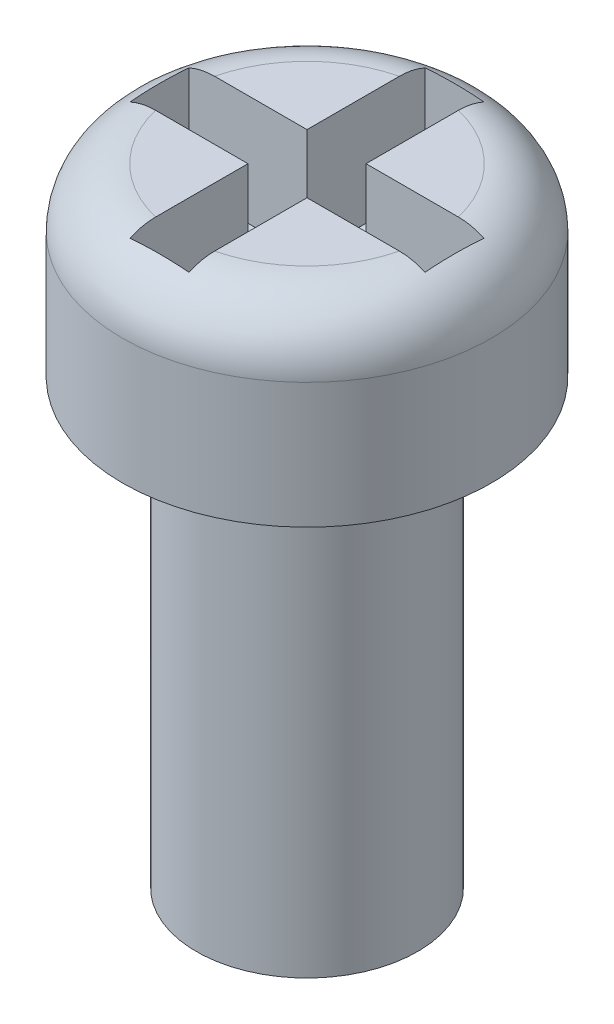
SolidWorks part; units mm, degrees
ref_plane "Alzado" through (0, 0, 0) normal (0, 0, 1) x (1, 0, 0)
ref_plane "Planta" through (0, 0, 0) normal (0, 1, 0) x (1, 0, 0)
ref_plane "Vista lateral" through (0, 0, 0) normal (1, 0, 0) x (0, 0, -1)
sketch "Croquis1" plane through (0, 0, 0) normal (0, 0, 1) x (1, 0, 0)
  line L0 (0, 0) -> (0, 8.5) construction
  line L1 (0, 0) -> (-1.5, 0)
  line L2 (-1.5, 0) -> (-1.5, 6)
  line L3 (-1.5, 6) -> (-2.5, 6)
  line L4 (-2.5, 6) -> (-2.5, 8.5)
  line L5 (-2.5, 8.5) -> (0, 8.5)
  line L6 (0, 0) -> (0, 8.5)
  dimension "D1" = 6
  dimension "D2" = 2.5
  dimension "D3" = 2.5
  dimension "D4" = 1.5
revolve "Revolución1" add sketch "Croquis1" angle 360 about L0
fillet "Redondeo1" radius 0.8 1 edges at (0, 8.5, -2.5)
sketch "Croquis2" plane through (0, 8.5, 0) normal (0, 1, 0) x (1, 0, 0)
  line L4 (0, -2) -> (0, 2) construction
  line L5 (-2, 0) -> (2, 0) construction
  line L6 (0.4, -2) -> (0.4, -0.4)
  line L7 (-2, -0.4) -> (-0.4, -0.4)
  line L8 (-0.4, -2) -> (-0.4, -0.4)
  line L9 (-2, 0.4) -> (-0.4, 0.4)
  line L10 (0.4, -2) -> (-0.4, -2)
  line L11 (0.4, 2) -> (-0.4, 2)
  line L12 (-2, -0.4) -> (-2, 0.4)
  line L13 (2, -0.4) -> (2, 0.4)
  line L14 (-0.4, 0.4) -> (-0.4, 2)
  line L15 (-0.4, -2) -> (-0.4, 2) construction
  line L16 (0.4, 0.4) -> (2, 0.4)
  line L17 (-2, 0.4) -> (2, 0.4) construction
  line L18 (0.4, 0.4) -> (0.4, 2)
  line L19 (0.4, -2) -> (0.4, 2) construction
  line L20 (0.4, -0.4) -> (2, -0.4)
  line L21 (-2, -0.4) -> (2, -0.4) construction
  point P1 (0, 0)
  point P2 (0, 0)
  point P11 (0, 0)
  dimension "D1" = 4
  dimension "D2" = 4
  dimension "D3" = 0.4
  dimension "D4" = 0.4
extrude "Cortar-Extruir1" cut sketch "Croquis2" against normal blind 1.5
